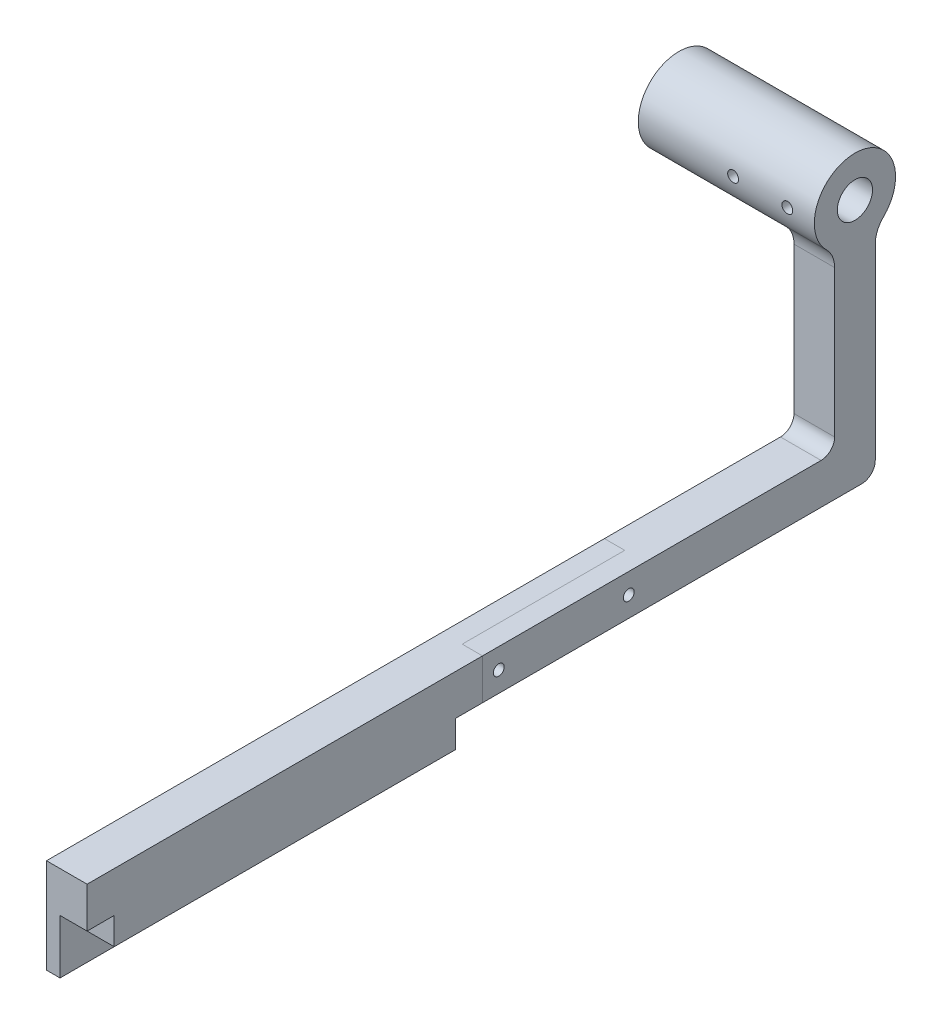
SolidWorks part; units mm, degrees
ref_plane "Front Plane" through (0, 0, 0) normal (0, 0, 1) x (1, 0, 0)
ref_plane "Top Plane" through (0, 0, 0) normal (0, 1, 0) x (1, 0, 0)
ref_plane "Right Plane" through (0, 0, 0) normal (1, 0, 0) x (0, 0, -1)
sketch "Sketch4" plane through (0, 0, 0) normal (1, 0, 0) x (0, 0, -1)
  line L0 (0, 10) -> (-10, 10)
  line L1 (0, 0) -> (126, 0)
  line L2 (0, 0) -> (0, 10)
  line L3 (0, 10) -> (126, 10) construction
  line L4 (126, 0) -> (126, 10)
  line L5 (-10, 10) -> (-10, 25)
  line L6 (-10, 25) -> (136, 25)
  line L7 (136, 25) -> (136, 10)
  line L8 (136, 10) -> (126, 10)
  dimension "D1" = 10
  dimension "D2" = 126
  dimension "D3" = 10
  dimension "D4" = 10
  dimension "D5" = 15
extrude "Boss-Extrude3" add sketch "Sketch4" along normal blind 10
sketch "Sketch8" plane through (0, 0, 0) normal (-1, 0, 0) x (0, 0, 1)
  line L1 (-136, 25) -> (10, 25)
  line L2 (-136, 25) -> (-136, 10)
  line L3 (-136, 10) -> (10, 10)
  line L4 (10, 25) -> (10, 10)
extrude "Boss-Extrude6" add sketch "Sketch8" along normal blind 5
sketch "Sketch9" plane through (0, 10, 0) normal (0, -1, 0) x (1, 0, 0)
  line L0 (10, -136) -> (-5, -136) construction
  line L1 (-5, 10) -> (0, 10)
  line L2 (-5, 10) -> (-5, -136)
  line L3 (-5, -136) -> (0, -136)
  line L4 (0, 10) -> (0, -136)
extrude "Boss-Extrude7" add sketch "Sketch9" along normal blind 20
sketch "Sketch10" plane through (0, 0, 0) normal (1, 0, 0) x (0, 0, -1)
  line L0 (0, 0) -> (0, -10) construction
  line L1 (136, -10) -> (-10, -10) construction
  line L2 (126, 0) -> (126, -10) construction
  line L3 (63, 0) -> (63, -10) construction
  line L4 (0, 0) -> (126, 0) construction
  circle A0 centre (15, -5) radius 2
  circle A1 centre (111, -5) radius 2
  dimension "D2" = 4
  dimension "D1" = 15
extrude "Cut-Extrude2" cut sketch "Sketch10" against normal blind 20
sketch "Sketch5" plane through (10, 0, 0) normal (1, 0, 0) x (0, 0, -1)
  line L0 (266, 95.52) -> (266, 25) construction
  line L1 (136, 10) -> (266, 10)
  line L2 (136, 10) -> (136, 25)
  line L3 (136, 25) -> (261, 25)
  line L4 (266, 10) -> (266, 25) construction
  line L5 (266, 10) -> (276, 10)
  line L6 (266, 10) -> (266, 95.52) construction
  line L7 (266, 95.52) -> (281, 95.52) construction
  line L8 (281, 10) -> (281, 95.52) construction
  line L9 (266, 84.1664) -> (266, 30)
  line L10 (281, 84.1664) -> (281, 15)
  circle A0 centre (273.5, 102.02) radius 6.5
  arc A1 (263, 91.3079) -> (284, 91.3079) centre (273.5, 102.02) cw
  arc A2 (284, 91.3079) -> (281, 84.1664) centre (291, 84.1664) ccw
  arc A3 (263, 91.3079) -> (266, 84.1664) centre (256, 84.1664) cw
  arc A4 (276, 10) -> (281, 15) centre (276, 15) ccw
  arc A5 (261, 25) -> (266, 30) centre (261, 30) ccw
  point P14 (281, 89.0296)
  point P17 (266, 89.0296)
  dimension "D5" = 13
  dimension "D6" = 15
  dimension "D7" = 10
  dimension "D8" = 5
  dimension "D1" = 130
  dimension "D2" = 15
  dimension "D3" = 15
  dimension "D4" = 85.52
  dimension "D9" = 7.5
extrude "Boss-Extrude4" add sketch "Sketch5" against normal blind 15
sketch "Sketch6" plane through (-5, 0, 0) normal (-1, 0, 0) x (0, 0, 1)
  circle A0 centre (-273.5, 102.02) radius 6.5
  circle A1 centre (-273.5, 102.02) radius 15
extrude "Boss-Extrude5" add sketch "Sketch6" along normal blind 50
ref_plane "Plane2" through (0, 0, -288.5) normal (0, 0, -1) x (-1, 0, 0)
ref_plane "Plane3" through (0, 0, -258.5) normal (0, 0, 1) x (1, 0, 0)
sketch "Sketch7" plane through (0, 0, -288.5) normal (0, 0, -1) x (-1, 0, 0)
  line L0 (-10, 117.02) -> (-10, 91.3079) construction
  circle A0 centre (20, 102.02) radius 2
  circle A1 centre (0, 102.02) radius 2
  dimension "D1" = 4
  dimension "D2" = 4
  dimension "D3" = 10
  dimension "D4" = 20
extrude "Cut-Extrude1" cut sketch "Sketch7" against normal blind 50
sketch "Sketch13" plane through (-5, 0, 0) normal (-1, 0, 0) x (0, 0, 1)
  line L0 (-196, 25) -> (-196, 10) construction
  line L1 (-136, 10) -> (-276, 10) construction
  line L2 (-136, 25) -> (-136, 10) construction
  circle A0 centre (-190, 17.5) radius 2
  circle A1 centre (-142, 17.5) radius 2
  dimension "D2" = 4
  dimension "D3" = 4
  dimension "D1" = 6
  dimension "D4" = 6
extrude "Cut-Extrude3" cut sketch "Sketch13" against normal blind 20
sketch "Sketch12" plane through (0, 25, 0) normal (0, 1, 0) x (1, 0, 0)
  line L0 (-5, 136) -> (10, 136) construction
  line L1 (-5, -10) -> (-5, 261) construction
  line L2 (10, 261) -> (10, -10) construction
  line L3 (10, -10) -> (-5, -10) construction
  line L4 (-5, 196) -> (10, 196) construction
  line L5 (2.5, 196) -> (2.5, 136)
  line L6 (2.5, 196) -> (-5, 196)
  line L7 (2.5, 136) -> (10, 136)
  dimension "D1" = 146
  dimension "D2" = 60
split "Split2" trim tools "Sketch12" bodies to split 112 resulting bodies 113 114
